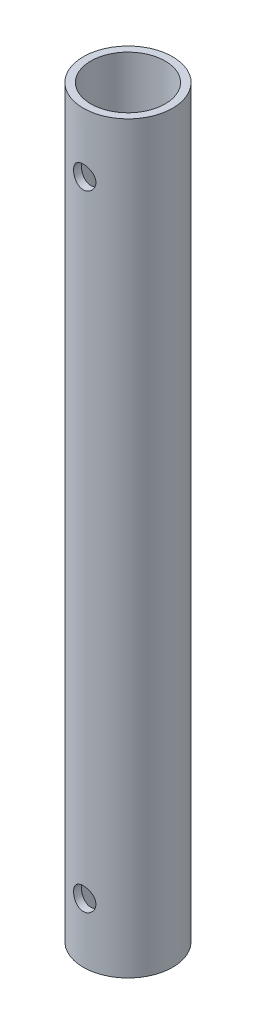
SolidWorks part; units mm, degrees
ref_plane "Ön Düzlem" through (0, 0, 0) normal (0, 0, 1) x (1, 0, 0)
ref_plane "Üst Düzlem" through (0, 0, 0) normal (0, 1, 0) x (1, 0, 0)
ref_plane "Sağ Düzlem" through (0, 0, 0) normal (1, 0, 0) x (0, 0, -1)
sketch "Sketch1" plane through (0, 0, 0) normal (0, 1, 0) x (1, 0, 0)
  circle A0 centre (0, 0) radius 6
  dimension "D1" = 12
sketch "Sketch2" plane through (0, 0, 0) normal (0, 0, 1) x (1, 0, 0)
  circle A0 centre (0, 8) radius 1.5
  dimension "D1" = 3
  dimension "D2" = 8
extrude "Extrude-Thin1" add sketch "Sketch1" along normal blind 100 thin thin type one direction reverse wall 1
extrude "Cut-Extrude2" cut sketch "Sketch2" against normal through all both and the other way through all
sketch "Sketch3" plane through (0, 0, 0) normal (0, 0, 1) x (1, 0, 0)
  line L0 (6, 100) -> (-6, 100) construction
  circle A0 centre (0, 92) radius 1.5
  dimension "D1" = 3
  dimension "D2" = 8
extrude "Cut-Extrude3" cut sketch "Sketch3" against normal through all both and the other way through all
